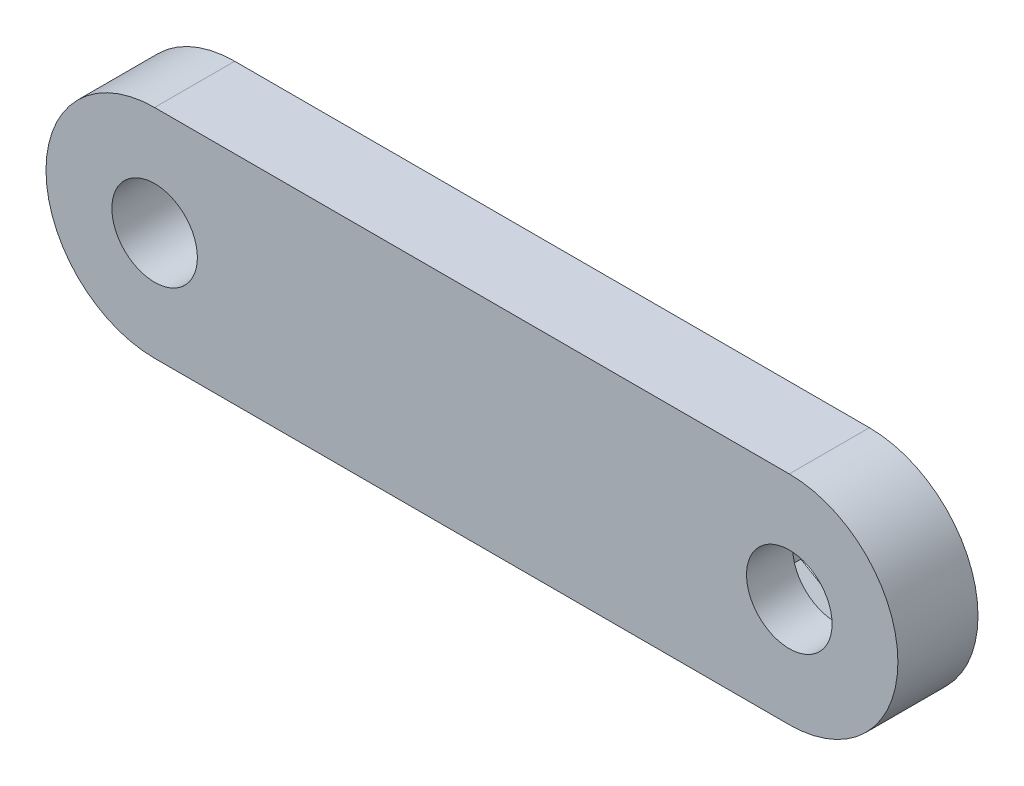
SolidWorks part; units mm, degrees
ref_plane "Front Plane" through (0, 0, 0) normal (0, 0, 1) x (1, 0, 0)
ref_plane "Top Plane" through (0, 0, 0) normal (0, 1, 0) x (1, 0, 0)
ref_plane "Right Plane" through (0, 0, 0) normal (1, 0, 0) x (0, 0, -1)
sketch "Sketch1" plane through (0, 0, 0) normal (0, 0, 1) x (1, 0, 0)
  line L0 (23.375, 0) -> (-23.375, 0) construction
  line L1 (23.375, -8) -> (-23.375, -8)
  line L2 (23.375, 8) -> (-23.375, 8)
  arc A0 (23.375, -8) -> (23.375, 8) centre (23.375, 0) ccw
  arc A1 (-23.375, 8) -> (-23.375, -8) centre (-23.375, 0) ccw
  circle A2 centre (23.375, 0) radius 3.15
  circle A3 centre (-23.375, 0) radius 3.15
  point P2 (0, 0)
  dimension "D2" = 6.3
  dimension "D1" = 16
  dimension "D3" = 46.75
extrude "Boss-Extrude1" add sketch "Sketch1" along normal blind 5.9
sketch "Sketch2" plane through (0, 0, 0) normal (0, 0, 1) x (1, 0, 0)
  line L0 (23.375, 8) -> (-23.375, 8) construction
  line L1 (23.375, 5.8312) -> (18.325, 2.9156)
  line L2 (18.325, 2.9156) -> (18.325, -2.9156)
  line L3 (18.325, -2.9156) -> (23.375, -5.8312)
  line L4 (23.375, -5.8312) -> (28.425, -2.9156)
  line L5 (28.425, -2.9156) -> (28.425, 2.9156)
  line L6 (28.425, 2.9156) -> (23.375, 5.8312)
  circle A0 centre (23.375, 0) radius 5.05 construction
  dimension "D1" = 10.1
extrude "Cut-Extrude2" cut sketch "Sketch2" along normal blind 2.5
move or copy body "Body-Move/Copy1" [suppressed] bodies to move or copy 101
